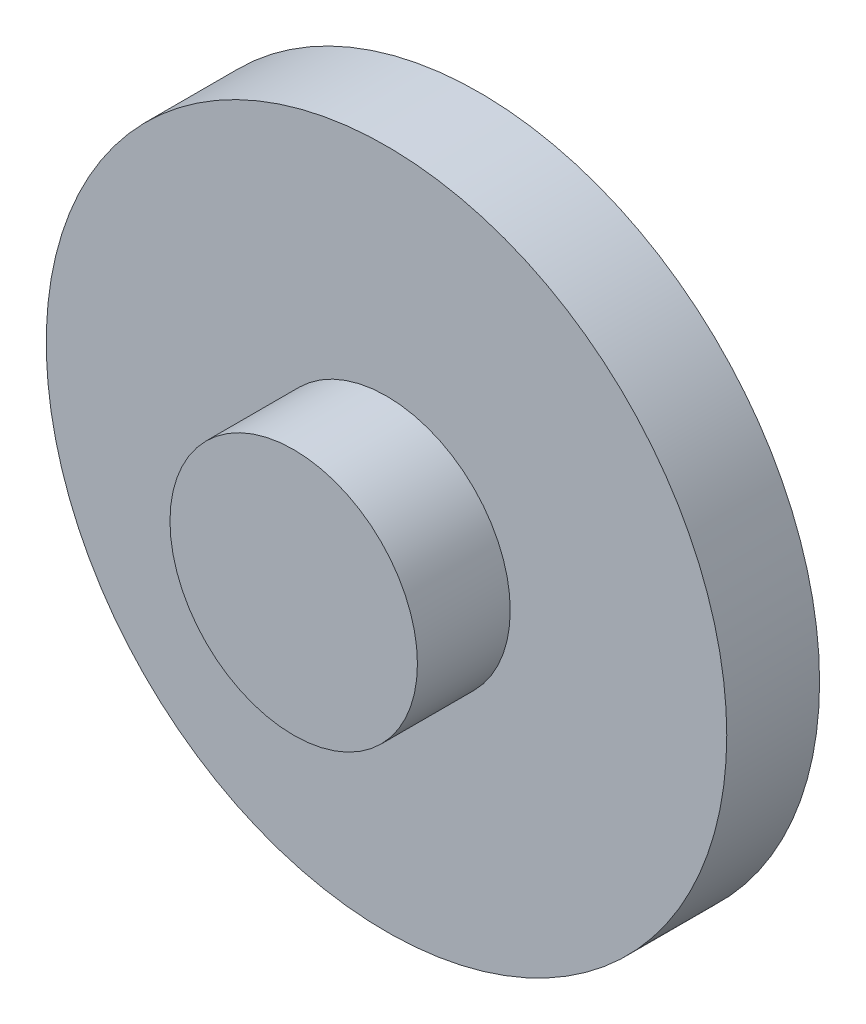
SolidWorks part; units mm, degrees
ref_plane "Front Plane" through (0, 0, 0) normal (0, 0, 1) x (1, 0, 0)
ref_plane "Top Plane" through (0, 0, 0) normal (0, 1, 0) x (1, 0, 0)
ref_plane "Right Plane" through (0, 0, 0) normal (1, 0, 0) x (0, 0, -1)
sketch "Sketch1" plane through (0, 0, 0) normal (0, 0, 1) x (1, 0, 0)
  circle A0 centre (0, 0) radius 11
  dimension "D1" = 22
extrude "Boss-Extrude1" add sketch "Sketch1" along normal blind 3
sketch "Sketch2" plane through (0, 0, 3) normal (0, 0, 1) x (1, 0, 0)
  circle A0 centre (0, 0) radius 4
  dimension "D1" = 8
extrude "Boss-Extrude2" add sketch "Sketch2" along normal blind 3
